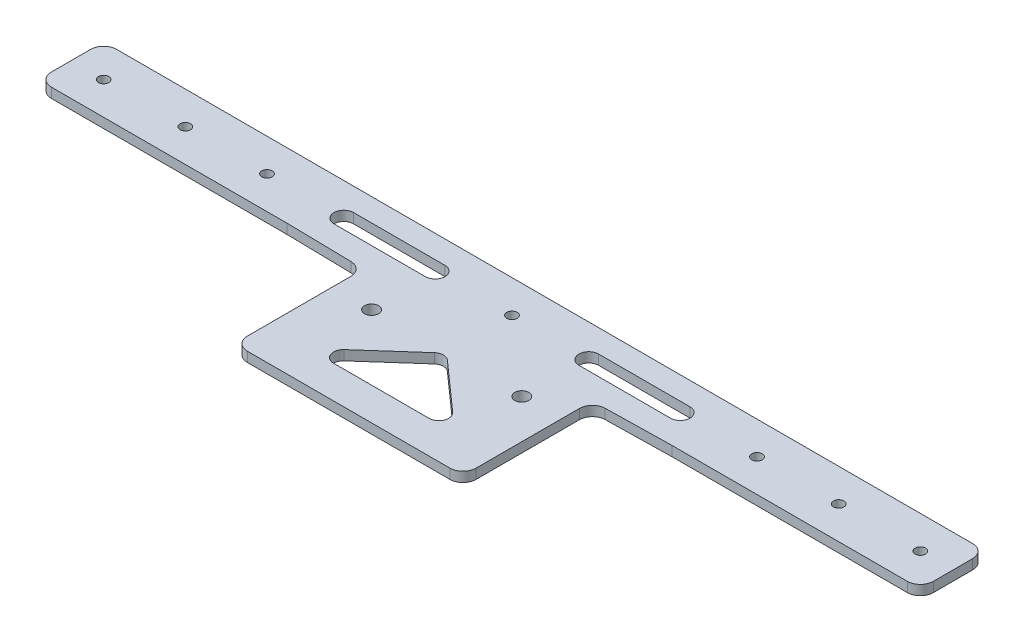
SolidWorks part; units mm, degrees
material "A-玻璃纤维"
ref_plane "前视基准面" through (0, 0, 0) normal (0, 0, 1) x (1, 0, 0)
ref_plane "上视基准面" through (0, 0, 0) normal (0, 1, 0) x (1, 0, 0)
ref_plane "右视基准面" through (0, 0, 0) normal (1, 0, 0) x (0, 0, -1)
sketch "草图1" plane through (0, 0, 0) normal (0, 1, 0) x (1, 0, 0)
  line L1 (-135, 30) -> (135, 30)
  line L2 (-135, 30) -> (-135, -30)
  line L3 (-135, -30) -> (135, -30)
  line L4 (135, 30) -> (135, -30)
  line L5 (-135, 30) -> (135, -30) construction
  line L6 (-135, -30) -> (135, 30) construction
  point P0 (0, 0)
  dimension "D1" = 270
  dimension "D2" = 60
extrude "凸台-拉伸1" add sketch "草图1" along normal blind 3
sketch "草图2" plane through (0, 3, 0) normal (0, 1, 0) x (1, 0, 0)
  line L0 (0, 30) -> (0, -30) construction
  line L1 (135, 30) -> (-135, 30) construction
  line L2 (-135, -30) -> (135, -30) construction
  line L3 (-135, 0) -> (135, 0) construction
  line L4 (-135, 30) -> (-135, -30) construction
  line L5 (135, -30) -> (135, 30) construction
  circle A0 centre (-23, 0) radius 2.15
  circle A1 centre (23, 0) radius 2.15
  circle A2 centre (-125, -20) radius 1.6
  circle A3 centre (-125, -60) radius 1.6
  circle A4 centre (125, -60) radius 1.6
  circle A5 centre (125, -20) radius 1.6
  dimension "D1" = 3.2
  dimension "D2" = 4.3
  dimension "D3" = 46
  dimension "D4" = 30
  dimension "D5" = 250
  dimension "D6" = 50
  dimension "D7" = 40
extrude "切除-拉伸1" cut sketch "草图2" against normal blind 3
sketch "草图3" plane through (0, 3, 0) normal (0, 1, 0) x (1, 0, 0)
  line L0 (0, 61.9673) -> (0, -75.2967) construction
  line L1 (-151.8321, 20) -> (163.9681, 20) construction
  line L2 (135, 30) -> (-135, 30) construction
  line L3 (125, -20) -> (125, 65.1087) construction
  circle A0 centre (125, 20) radius 1.6
  circle A1 centre (100, 20) radius 1.6
  circle A2 centre (75, 20) radius 1.6
  circle A3 centre (0, 20) radius 1.6
  circle A5 centre (-75, 20) radius 1.6
  circle A6 centre (-100, 20) radius 1.6
  circle A7 centre (-125, 20) radius 1.6
  dimension "D2" = 25
  dimension "D3" = 50
  dimension "D4" = 3.2
  dimension "D1" = 10
extrude "切除-拉伸2" cut sketch "草图3" against normal blind 10
sketch "草图4" plane through (0, 3, 0) normal (0, 1, 0) x (1, 0, 0)
  line L0 (0, 87.4916) -> (0, -79.5507) construction
  line L1 (-114.8366, 15) -> (-115, 14.9285) construction
  line L2 (-112.8325, 10.4192) -> (-112.9959, 10.3477)
  line L3 (-116.8407, 19.5808) -> (-117.0041, 19.5093)
  line L4 (-81.7754, 12) -> (-115, -2.5358) construction
  line L5 (-79.7713, 7.4192) -> (-112.9959, -7.1165)
  line L6 (-83.7795, 16.5808) -> (-117.0041, 2.045)
  line L7 (-135, 15) -> (135, 15) construction
  line L8 (-135, 30) -> (-135, -30) construction
  line L9 (135, -30) -> (135, 30) construction
  line L10 (-115, 30) -> (-115, -30) construction
  line L11 (135, 30) -> (-135, 30) construction
  line L12 (-135, -30) -> (135, -30) construction
  line L13 (-35, 15) -> (-115, -20) construction
  line L14 (-32.9959, 10.4192) -> (-112.9959, -24.5808)
  line L15 (-37.0041, 19.5808) -> (-117.0041, -15.4192)
  line L16 (-150.3212, -20) -> (137.4886, -20) construction
  line L17 (-35, 69.0212) -> (-35, -65.7402) construction
  line L18 (-35, -5.4642) -> (-68.2246, -20) construction
  line L19 (-32.9959, -10.045) -> (-66.2205, -24.5808)
  line L20 (-37.0041, -0.8835) -> (-70.2287, -15.4192)
  line L21 (-35, -19.9285) -> (-35.1634, -20) construction
  line L22 (-32.9959, -24.5093) -> (-33.1593, -24.5808)
  line L23 (-37.0041, -15.3477) -> (-37.1675, -15.4192)
  line L24 (35, -19.9285) -> (35.1634, -20) construction
  line L25 (32.9959, -24.5093) -> (33.1593, -24.5808)
  line L26 (37.0041, -15.3477) -> (37.1675, -15.4192)
  line L27 (35, -5.4642) -> (68.2246, -20) construction
  line L28 (32.9959, -10.045) -> (66.2205, -24.5808)
  line L29 (37.0041, -0.8835) -> (70.2287, -15.4192)
  line L30 (35, 15) -> (115, -20) construction
  line L31 (32.9959, 10.4192) -> (112.9959, -24.5808)
  line L32 (37.0041, 19.5808) -> (117.0041, -15.4192)
  line L33 (81.7754, 12) -> (115, -2.5358) construction
  line L34 (79.7713, 7.4192) -> (112.9959, -7.1165)
  line L35 (83.7795, 16.5808) -> (117.0041, 2.045)
  line L36 (114.8366, 15) -> (115, 14.9285) construction
  line L37 (112.8325, 10.4192) -> (112.9959, 10.3477)
  line L38 (116.8407, 19.5808) -> (117.0041, 19.5093)
  line L39 (0, -20) -> (-22.5, -20)
  line L40 (-22.5, -20) -> (0, 0)
  line L41 (0, 0) -> (22.5, -20)
  line L42 (22.5, -20) -> (0, -20)
  line L43 (-135, -30) -> (135, -30) construction
  arc A0 (-112.8325, 10.4192) -> (-116.8407, 19.5808) centre (-114.8366, 15) ccw
  arc A1 (-117.0041, 19.5093) -> (-112.9959, 10.3477) centre (-115, 14.9285) ccw
  arc A2 (-79.7713, 7.4192) -> (-83.7795, 16.5808) centre (-81.7754, 12) ccw
  arc A3 (-117.0041, 2.045) -> (-112.9959, -7.1165) centre (-115, -2.5358) ccw
  arc A4 (-32.9959, 10.4192) -> (-37.0041, 19.5808) centre (-35, 15) ccw
  arc A5 (-117.0041, -15.4192) -> (-112.9959, -24.5808) centre (-115, -20) ccw
  arc A6 (-32.9959, -10.045) -> (-37.0041, -0.8835) centre (-35, -5.4642) ccw
  arc A7 (-70.2287, -15.4192) -> (-66.2205, -24.5808) centre (-68.2246, -20) ccw
  arc A8 (-32.9959, -24.5093) -> (-37.0041, -15.3477) centre (-35, -19.9285) ccw
  arc A9 (-37.1675, -15.4192) -> (-33.1593, -24.5808) centre (-35.1634, -20) ccw
  arc A10 (32.9959, -24.5093) -> (37.0041, -15.3477) centre (35, -19.9285) cw
  arc A11 (37.1675, -15.4192) -> (33.1593, -24.5808) centre (35.1634, -20) cw
  arc A12 (32.9959, -10.045) -> (37.0041, -0.8835) centre (35, -5.4642) cw
  arc A13 (70.2287, -15.4192) -> (66.2205, -24.5808) centre (68.2246, -20) cw
  arc A14 (32.9959, 10.4192) -> (37.0041, 19.5808) centre (35, 15) cw
  arc A15 (117.0041, -15.4192) -> (112.9959, -24.5808) centre (115, -20) cw
  arc A16 (79.7713, 7.4192) -> (83.7795, 16.5808) centre (81.7754, 12) cw
  arc A17 (117.0041, 2.045) -> (112.9959, -7.1165) centre (115, -2.5358) cw
  arc A18 (112.8325, 10.4192) -> (116.8407, 19.5808) centre (114.8366, 15) cw
  arc A19 (117.0041, 19.5093) -> (112.9959, 10.3477) centre (115, 14.9285) cw
  point P5 (-114.9183, 14.9642)
  point P10 (-98.3877, 4.7321)
  point P23 (-75, -2.5)
  point P42 (-51.6123, -12.7321)
  point P47 (-35.0817, -19.9642)
  point P56 (35.0817, -19.9642)
  point P63 (51.6123, -12.7321)
  point P70 (75, -2.5)
  point P77 (98.3877, 4.7321)
  point P84 (114.9183, 14.9642)
  dimension "D1" = 10
  dimension "D2" = 6
  dimension "D3" = 6
  dimension "D4" = 15
  dimension "D5" = 10
  dimension "D6" = 20
  dimension "D7" = 35
  dimension "D8" = 45
  dimension "D9" = 18
extrude "切除-拉伸3" cut sketch "草图4" against normal blind 10
fillet "圆角1" radius 3 3 edges at (22.5, 1.5, 20) (-22.5, 1.5, 20) (0, 1.5, 0)
fillet "圆角2" radius 4 4 edges at (135, 1.5, 30) (-135, 1.5, -30) (135, 1.5, -30) (-135, 1.5, 30)
sketch "草图5" plane through (0, 3, 0) normal (0, 1, 0) x (1, 0, 0)
  line L0 (0, 0) -> (0, 88.2804) construction
  line L1 (-131, -30) -> (131, -30) construction
  line L2 (-35, -30) -> (-135, -30)
  line L3 (-35, -30) -> (-35, 10)
  line L4 (-35, 10) -> (-135, 10)
  line L5 (-135, -30) -> (-135, 10)
  line L6 (-135, 26) -> (-135, -26) construction
  line L7 (131, 30) -> (-131, 30) construction
  line L8 (135, -30) -> (135, 10)
  line L9 (35, 10) -> (135, 10)
  line L10 (35, -30) -> (35, 10)
  line L11 (35, -30) -> (135, -30)
  dimension "D1" = 20
  dimension "D2" = 35
extrude "切除-拉伸4" cut sketch "草图5" against normal blind 10
sketch "草图6" plane through (0, 3, 0) normal (0, 1, 0) x (1, 0, 0)
  line L2 (-111.5199, 10) -> (-118.1532, 10)
  arc A0 (-111.5199, 10) -> (-118.1532, 10) centre (-114.8366, 15) ccw
extrude "凸台-拉伸2" add sketch "草图6" against normal up to surface (3 mm away) up to face at (0, 0, -4.1537)
sketch "草图7" plane through (0, 3, 0) normal (0, 1, 0) x (1, 0, 0)
  line L0 (-98.8213, 10) -> (-83.7795, 16.5808)
  line L1 (-77.1929, 10) -> (-98.8213, 10)
  arc A0 (-83.7795, 16.5808) -> (-77.1929, 10) centre (-81.7754, 12) cw
  dimension "D1" = 5
extrude "凸台-拉伸9" add sketch "草图7" against normal blind 3
sketch "草图8" plane through (0, 3, 0) normal (0, 1, 0) x (1, 0, 0)
  line L0 (-58.903, 10) -> (-35, 9.5424)
  line L1 (-35, 9.5424) -> (-32.9959, 10.4192)
  line L2 (-58.903, 10) -> (-37.0041, 19.5808)
  arc A0 (-32.9959, 10.4192) -> (-37.0041, 19.5808) centre (-35, 15) ccw
  dimension "D1" = 5
extrude "凸台-拉伸10" add sketch "草图8" against normal blind 3
sketch "草图9" plane through (0, 3, 0) normal (0, 1, 0) x (1, 0, 0)
  line L0 (-35, -0.4642) -> (-35, -10.9218)
  line L1 (-35, -10.9218) -> (-32.9959, -10.045)
  arc A0 (-32.9959, -10.045) -> (-35, -0.4642) centre (-35, -5.4642) ccw
  dimension "D1" = 5
extrude "凸台-拉伸11" add sketch "草图9" against normal blind 3
sketch "草图10" plane through (0, 3, 0) normal (0, 1, 0) x (1, 0, 0)
  line L0 (-35, -14.9285) -> (-35, -24.9973)
  arc A0 (-35, -14.9285) -> (-35, -24.9973) centre (-35, -19.9629) cw
  dimension "D1" = 5.0344
extrude "凸台-拉伸13" add sketch "草图10" against normal blind 3
sketch "草图11" plane through (0, 3, 0) normal (0, 1, 0) x (1, 0, 0)
  line L0 (35, -0.4642) -> (35, -10.9218)
  arc A0 (35, -0.4642) -> (35, -10.9218) centre (35, -5.693) ccw
  dimension "D1" = 5.2288
extrude "凸台-拉伸14" add sketch "草图11" against normal blind 3
sketch "草图12" plane through (0, 3, 0) normal (0, 1, 0) x (1, 0, 0)
  line L0 (35, -14.9285) -> (35, -24.9973)
  arc A0 (35, -14.9285) -> (35, -24.9973) centre (35, -19.9629) ccw
  dimension "D1" = 5.0344
extrude "凸台-拉伸16" add sketch "草图12" against normal blind 3
sketch "草图13" plane through (0, 3, 0) normal (0, 1, 0) x (1, 0, 0)
  line L0 (58.903, 10) -> (37.0041, 19.5808)
  line L1 (35, 9.5424) -> (32.9959, 10.4192)
  line L2 (58.903, 10) -> (35, 9.5424)
  arc A0 (37.0041, 19.5808) -> (32.9959, 10.4192) centre (35, 15) ccw
  dimension "D1" = 5
extrude "凸台-拉伸17" add sketch "草图13" against normal blind 3
sketch "草图14" plane through (0, 3, 0) normal (0, 1, 0) x (1, 0, 0)
  line L0 (98.8213, 10) -> (83.7795, 16.5808)
  line L1 (98.8213, 10) -> (77.1929, 10)
  arc A0 (83.7795, 16.5808) -> (77.1929, 10) centre (81.7754, 12) ccw
  dimension "D1" = 5
extrude "凸台-拉伸18" add sketch "草图14" against normal blind 3
sketch "草图15" plane through (0, 3, 0) normal (0, 1, 0) x (1, 0, 0)
  line L2 (116.7324, 10) -> (112.9407, 10)
  arc A0 (116.7324, 10) -> (112.9407, 10) centre (114.8366, 15) ccw
extrude "凸台-拉伸19" add sketch "草图15" against normal blind 3
sketch "草图16" plane through (0, 3, 0) normal (0, 1, 0) x (1, 0, 0)
  line L0 (0, 20) -> (-75, 20) construction
  line L1 (-135, 18) -> (82.6608, 18) construction
  line L2 (-135, 26) -> (-135, 10) construction
  line L3 (0, -30) -> (0, 30) construction
  line L4 (-35, -30) -> (35, -30) construction
  line L5 (131, 30) -> (-131, 30) construction
  line L6 (-37.5, 20) -> (-37.5, 9.5903) construction
  line L7 (-58.903, 10) -> (-35, 9.5424) construction
  line L8 (-23.5, 20) -> (-51.5, 20) construction
  line L9 (23.5, 20) -> (51.5, 20) construction
  line L10 (-23.5, 17) -> (-51.5, 17)
  line L11 (-23.5, 23) -> (-51.5, 23)
  line L12 (23.5, 17) -> (51.5, 17)
  line L13 (23.5, 23) -> (51.5, 23)
  arc A0 (-23.5, 17) -> (-23.5, 23) centre (-23.5, 20) ccw
  arc A1 (-51.5, 23) -> (-51.5, 17) centre (-51.5, 20) ccw
  arc A2 (23.5, 17) -> (23.5, 23) centre (23.5, 20) cw
  arc A3 (51.5, 23) -> (51.5, 17) centre (51.5, 20) cw
  point P22 (-37.5, 20)
  point P27 (37.5, 20)
extrude "切除-拉伸5" cut sketch "草图16" against normal through all
fillet "圆角4" radius 4 6 edges at (135, 1.5, -10) (35, 1.5, -9.5424) (35, 1.5, 30) (-35, 1.5, -9.5424) (-35, 1.5, 30) (-135, 1.5, -10)
